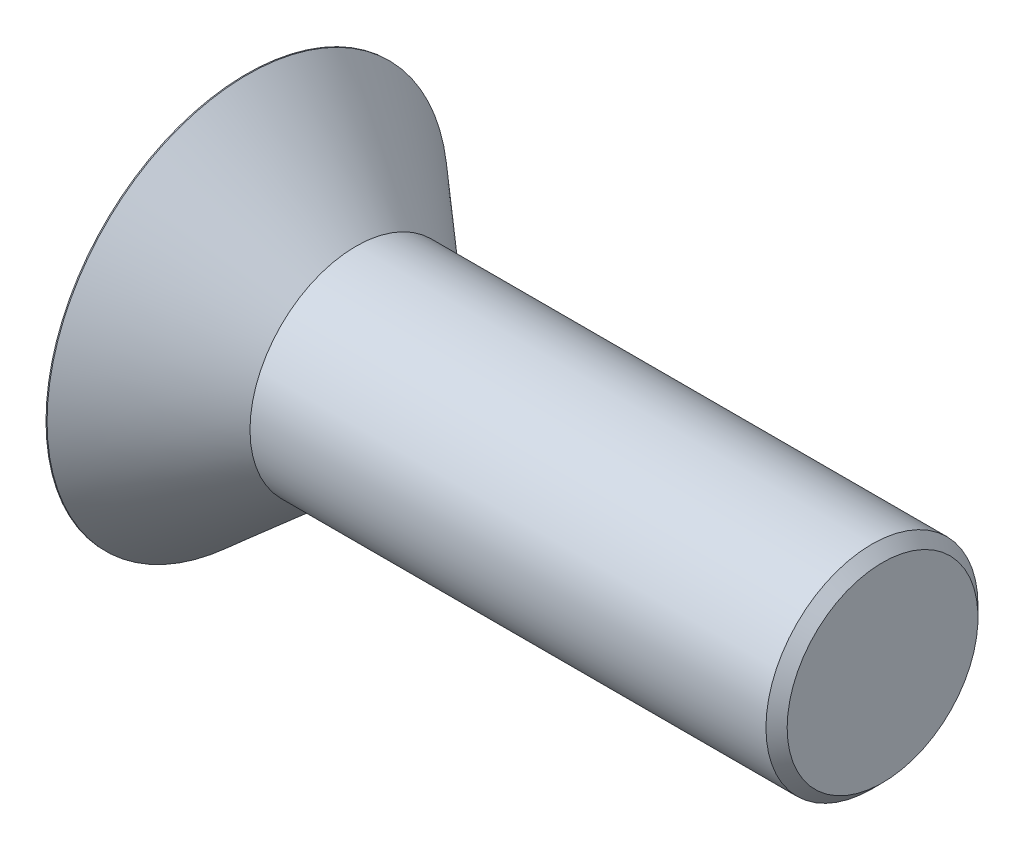
SolidWorks part; units mm, degrees
ref_plane "Plane1" through (0, 0, 0) normal (0, 0, 1) x (1, 0, 0)
ref_plane "Plane2" through (0, 0, 0) normal (0, 1, 0) x (1, 0, 0)
ref_plane "Plane3" through (0, 0, 0) normal (1, 0, 0) x (0, 0, -1)
sketch "BodySke" plane through (0, 0, 0) normal (0, 0, 1) x (1, 0, 0)
  line L0 (0, 0) -> (0, 24.003)
  line L1 (0.127, 24.003) -> (13.1296, 12.7)
  line L2 (0, 24.003) -> (0.127, 24.003)
  line L3 (13.1296, 12.7) -> (74.93, 12.7)
  line L4 (76.2, 11.43) -> (76.2, 0)
  line L5 (76.2, 0) -> (0, 0)
  line L6 (0, 0) -> (127, 0) construction
  line L7 (0.127, -24.003) -> (13.1296, -12.7) construction
  line L8 (76.2, 11.43) -> (74.93, 12.7)
  line L9 (0, -24.003) -> (0.127, -24.003) construction
  line L10 (76.2, -11.43) -> (74.93, -12.7) construction
  line L11 (15.2378, 19.05) -> (15.2378, -3.175) construction
  line L12 (50.8, 19.05) -> (50.8, -3.175) construction
  dimension "D1" = 0.127
  dimension "Diameter" = 25.4
  dimension "Length" = 76.2
  dimension "Body_ch_ang" = 45
  dimension "Head_dia" = 48.006
  dimension "Minor_dia" = 22.86
  dimension "Head_ang" = 82
  dimension "Advance" = 2.1082
  dimension "Thread_nom" = 25.4
revolve "BaseBody" add sketch "BodySke" angle 360 about L6
cosmetic thread "ThreadCosmetic" [suppressed] parameters "Thread_length"=25.4, "Thread_minor"=22.86
sketch "Sketch2" plane through (0, 0, 0) normal (0, 0, 1) x (1, 0, 0)
  line L0 (0, 7.9375) -> (7.5438, 7.9375)
  line L1 (7.5438, 7.9375) -> (12.1265, 0)
  line L2 (0, 0) -> (127, 0) construction
  line L3 (12.1265, 0) -> (0, 0)
  line L4 (0, 0) -> (0, 7.9375)
  line L5 (0, -7.9375) -> (7.5438, -7.9375) construction
  line L6 (0, 0) -> (47.625, 0) construction
  line L8 (0, 24.003) -> (0, -24.003) construction
  dimension "D2" = 60
  dimension "PreBroach_depth" = 7.5438
  dimension "PreBroach_dia" = 15.875
revolve "PreBroach" cut sketch "Sketch2" angle 360 about L6
sketch "Sketch3" plane through (0, 0, 0) normal (-1, 0, 0) x (0, 0, 1)
  line L0 (-7.9375, -4.5827) -> (-7.9375, 4.5827)
  line L1 (-7.9375, 4.5827) -> (0, 9.1654)
  line L2 (0, 9.1654) -> (7.9375, 4.5827)
  line L3 (7.9375, 4.5827) -> (7.9375, -4.5827)
  line L4 (7.9375, -4.5827) -> (0, -9.1654)
  line L5 (0, -9.1654) -> (-7.9375, -4.5827)
  dimension "D1" = 7.9375
  dimension "D2" = 7.9375
  dimension "D3" = 15.875
  dimension "Hex_size" = 15.875
extrude "Hex" cut sketch "Sketch3" against normal blind 7.5438
sketch "Sketch4" plane through (0, 0, 0) normal (-1, 0, 0) x (0, 0, 1)
  line L0 (0, 0) -> (10.1727, 0)
  line L1 (0, 0) -> (6.1484, 3.5498) construction
  line L2 (0, 0) -> (5.0863, 8.8098)
  line L3 (8.4417, 2.1022) -> (9.7612, 2.864)
  line L4 (6.0414, 6.2596) -> (7.3609, 7.0215)
  arc A0 (8.4417, 2.1022) -> (6.0414, 6.2596) centre (0, 0) ccw
  arc A1 (10.1727, 0) -> (9.7612, 2.864) centre (0, 0) ccw
  arc A2 (5.0863, 8.8098) -> (7.3609, 7.0215) centre (0, 0) cw
  dimension "D1" = 30
  dimension "Spline_n_dim" = 17.399
  dimension "Spline_m_dim" = 20.3454
  dimension "D2" = 60
  dimension "D3" = 2.4003
  dimension "Spline_p_dim" = 4.8006
extrude "Spline" [suppressed] cut sketch "Sketch4" against normal blind 7.5438
pattern_circular "CirPattern1" [suppressed] count 6 every 60 about axis through (0, 0, 0) along (1, 0, 0)
sketch "ThdSchSke" plane through (0, 0, 0) normal (0, 0, 1) x (1, 0, 0)
  line L0 (50.8, -11.43) -> (49.9108, -12.7)
  line L1 (50.8, -11.43) -> (51.6893, -12.7)
  line L2 (51.6893, -12.7) -> (51.6893, -15.875)
  line L3 (-3.175, 0) -> (5.1513, 0) construction
  line L4 (0, 24.003) -> (0, -24.003) construction
  line L5 (51.6893, -15.875) -> (49.9108, -15.875)
  line L6 (49.9108, -15.875) -> (49.9108, -12.7)
  dimension "Thread_minor" = 22.86
  dimension "Diameter" = 25.4
  dimension "Start" = 50.8
  dimension "SideAngle" = 55
  dimension "VeeAngle" = 70
  dimension "Overcut" = 31.75
revolve "ThreadSchematic" [suppressed] cut sketch "ThdSchSke" angle 360 about L3
pattern_linear "ThdSchPat" [suppressed]
equation "\"D3@Sketch4\" = \"Spline_p_dim@Sketch4\" / 2"
equation "\"Thread_minor@ThreadCosmetic\"  =  \"Minor_dia@BodySke\""
equation "\"D2@CirPattern1\" = 360 / \"Num_teeth@CirPattern1\""
equation "\"D1@Sketch3\" = \"Hex_size@Sketch3\" / 2"
equation "\"D2@Sketch3\" = \"D1@Sketch3\""
equation "\"D3@Sketch3\" = \"Hex_size@Sketch3\""
equation "\"Thread_length@ThreadCosmetic\" = ((sgn( (\"Length@BodySke\" - \"Advance@BodySke\" - ( ( ( \"Head_dia@BodySke\" - \"Diameter@BodySke\" ) * 0.5 ) / tan( \"Head_ang@BodySke\" * 0.008726646 ) ) ) - \"Thread_nom@BodySke\" )-1)*( (\"Length@BodySke\" - \"Advance@BodySke\" - ( ( ( \"Head_dia@BodySke\" - \"Diameter@BodySke\" ) "
equation "\"Thread_minor@ThdSchSke\" = \"Minor_dia@BodySke\""
equation "\"Diameter@ThdSchSke\" = \"Diameter@BodySke\""
equation "\"Overcut@ThdSchSke\" = \"Diameter@BodySke\" * 1.25"
equation "\"Start@ThdSchSke\" = 0.000001 + \"Length@BodySke\" - \"Thread_length@ThreadCosmetic\"  '---Countersunk---"
equation "\"Num_threads@ThdSchPat\" = int( \"Thread_length@ThreadCosmetic\" / \"Advance@BodySke\" + 0.999 )  + 1"
equation "\"Advance@ThdSchPat\" = \"Thread_length@ThreadCosmetic\" /  (\"Num_threads@ThdSchPat\" - 1) 'relax it"
equation "\"Num_threads@ThdSchPat\" = \"Num_threads@ThdSchPat\" - sgn( \"Num_threads@ThdSchPat\" - 1) '---chamfered tips only---"
